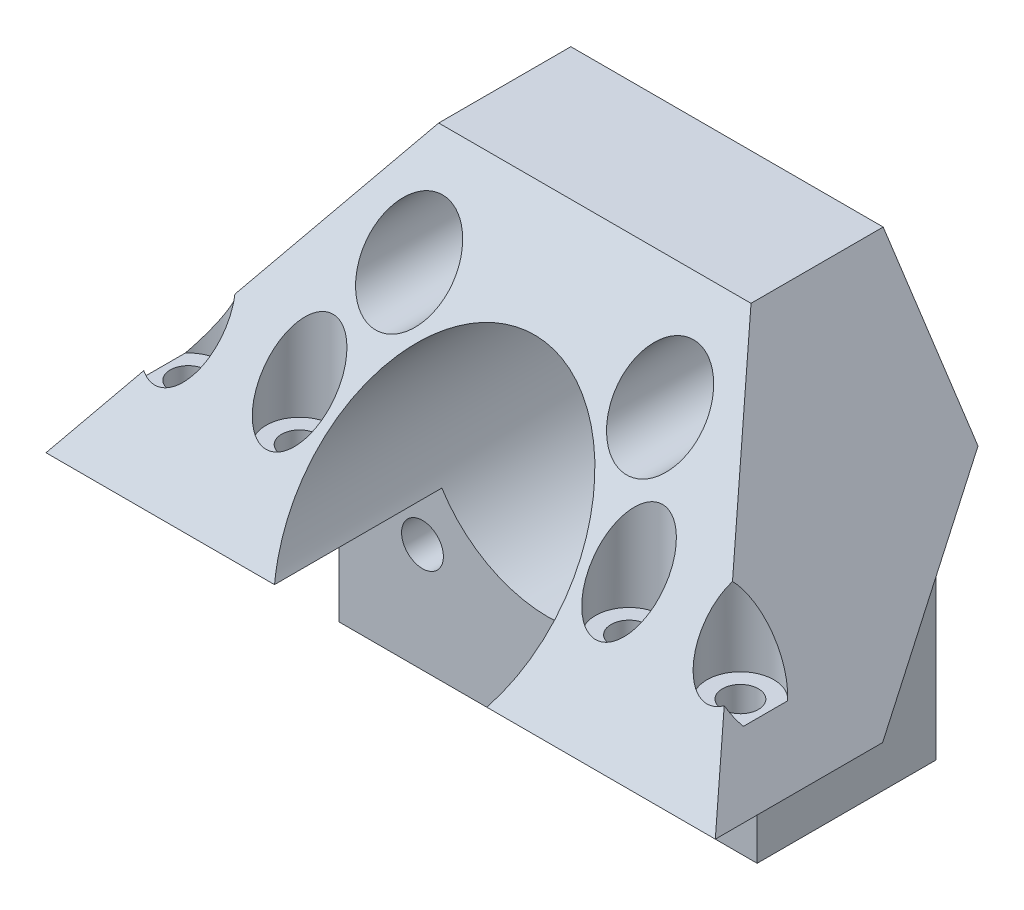
SolidWorks part; units mm, degrees
ref_plane "Front Plane" through (0, 0, 0) normal (0, 0, 1) x (1, 0, 0)
ref_plane "Top Plane" through (0, 0, 0) normal (0, 1, 0) x (1, 0, 0)
ref_plane "Right Plane" through (0, 0, 0) normal (1, 0, 0) x (0, 0, -1)
sketch "Sketch1" plane through (0, 0, 0) normal (0, 0, 1) x (1, 0, 0)
  line L1 (-10.526, 82.334) -> (-411.1387, 82.334) construction
  line L4 (-96.1387, 84.334) -> (-46.1387, 84.334)
  line L5 (-46.1387, 84.334) -> (-46.1387, 131.334)
  line L6 (-49.1387, 134.334) -> (-93.1387, 134.334)
  line L7 (-96.1387, 131.334) -> (-96.1387, 84.334)
  line L8 (-96.1387, 82.334) -> (-46.1387, 82.334)
  line L9 (-46.1387, 82.334) -> (-46.1387, 131.334)
  line L10 (-49.1387, 134.334) -> (-93.1387, 134.334)
  line L11 (-96.1387, 131.334) -> (-96.1387, 82.334)
  arc A0 (-71.1387, 95.334) -> (-71.1387, 125.334) centre (-71.1387, 110.334) ccw construction
  arc A1 (-71.1387, 125.334) -> (-71.1387, 95.334) centre (-71.1387, 110.334) ccw construction
  arc A2 (-46.1387, 131.334) -> (-49.1387, 134.334) centre (-49.1387, 131.334) ccw
  arc A3 (-93.1387, 134.334) -> (-96.1387, 131.334) centre (-93.1387, 131.334) ccw
  arc A4 (-46.1387, 131.334) -> (-49.1387, 134.334) centre (-49.1387, 131.334) ccw
  arc A5 (-93.1387, 134.334) -> (-96.1387, 131.334) centre (-93.1387, 131.334) ccw
  arc A6 (-56.1387, 127.834) -> (-56.1387, 122.834) centre (-56.1387, 125.334) ccw construction
  arc A7 (-56.1387, 122.834) -> (-56.1387, 127.834) centre (-56.1387, 125.334) ccw construction
  arc A8 (-86.1387, 122.834) -> (-86.1387, 127.834) centre (-86.1387, 125.334) ccw construction
  arc A9 (-86.1387, 127.834) -> (-86.1387, 122.834) centre (-86.1387, 125.334) ccw construction
  arc A10 (-56.1387, 97.834) -> (-56.1387, 92.834) centre (-56.1387, 95.334) ccw construction
  arc A11 (-56.1387, 92.834) -> (-56.1387, 97.834) centre (-56.1387, 95.334) ccw construction
  arc A12 (-86.1387, 97.834) -> (-86.1387, 92.834) centre (-86.1387, 95.334) ccw construction
  arc A13 (-86.1387, 92.834) -> (-86.1387, 97.834) centre (-86.1387, 95.334) ccw construction
  arc A14 (-86.1387, 92.834) -> (-86.1387, 97.834) centre (-86.1387, 95.334) ccw
  arc A15 (-86.1387, 97.834) -> (-86.1387, 92.834) centre (-86.1387, 95.334) ccw
  arc A16 (-56.1387, 92.834) -> (-56.1387, 97.834) centre (-56.1387, 95.334) ccw
  arc A17 (-56.1387, 97.834) -> (-56.1387, 92.834) centre (-56.1387, 95.334) ccw
  arc A18 (-86.1387, 127.834) -> (-86.1387, 122.834) centre (-86.1387, 125.334) ccw
  arc A19 (-86.1387, 122.834) -> (-86.1387, 127.834) centre (-86.1387, 125.334) ccw
  arc A20 (-56.1387, 122.834) -> (-56.1387, 127.834) centre (-56.1387, 125.334) ccw
  arc A21 (-56.1387, 127.834) -> (-56.1387, 122.834) centre (-56.1387, 125.334) ccw
  arc A22 (-71.1387, 125.334) -> (-71.1387, 95.334) centre (-71.1387, 110.334) ccw
  arc A23 (-71.1387, 95.334) -> (-71.1387, 125.334) centre (-71.1387, 110.334) ccw
  dimension "D1" = 0
extrude "Extrude1" add sketch "Sketch1" along normal up to vertex (21.3971 mm away)
sketch "Sketch3" plane through (0, 102.334, 0) normal (0, 1, 0) x (1, 0, 0)
  line L0 (-10.526, -21.3971) -> (-391.1387, -21.3971) construction
  line L1 (-31.1387, -21.3971) -> (-111.1387, -21.3971)
  line L2 (-31.1387, -21.3971) -> (-31.1387, -41.3971)
  line L3 (-31.1387, -41.3971) -> (-111.1387, -41.3971)
  line L4 (-111.1387, -21.3971) -> (-111.1387, -41.3971)
  line L5 (-10.526, -41.3971) -> (-411.1387, -41.3971) construction
  line L6 (-96.1387, -21.3971) -> (-96.1387, 0) construction
  line L7 (-46.1387, -21.3971) -> (-46.1387, 0) construction
  dimension "D1" = 15
  dimension "D2" = 15
ref_plane "Plane1" through (0, 117.334, 0) normal (0, 1, 0) x (1, 0, 0)
sketch "Sketch4" plane through (0, 117.334, 0) normal (0, 1, 0) x (1, 0, 0)
  line L0 (-46.1387, -21.3971) -> (-46.1387, 0) construction
  line L1 (-41.1387, 0) -> (-101.1387, 0)
  line L2 (-41.1387, 0) -> (-41.1387, -29.3971)
  line L3 (-41.1387, -29.3971) -> (-101.1387, -29.3971)
  line L4 (-101.1387, 0) -> (-101.1387, -29.3971)
  line L5 (-96.1387, -21.3971) -> (-96.1387, 0) construction
  line L6 (-96.1387, -21.3971) -> (-46.1387, -21.3971) construction
  line L7 (-96.1387, 0) -> (-46.1387, 0) construction
  dimension "D1" = 5
  dimension "D2" = 5
  dimension "D3" = 8
loft "Loft1" add profiles "Sketch4", "Sketch3"
sketch "Sketch5" plane through (25.6735, 17.1157, 0) normal (0.8321, 0.5547, 0) x (0, 0, -1)
  line L0 (-29.3971, 120.4474) -> (-15.1156, 141.9028)
  line L1 (-29.3971, 120.4474) -> (-41.3971, 102.4197) construction
  line L2 (0, 120.4474) -> (0, 141.9028)
  line L3 (0, 139.0299) -> (0, 163.4367) construction
  line L4 (0, 141.9028) -> (-15.1156, 141.9028)
  line L5 (-29.3971, 120.4474) -> (0, 120.4474)
extrude "Extrude2" add sketch "Sketch5" against normal blind 10
ref_plane "Plane2" through (-71.1387, 0, 0) normal (1, 0, 0) x (0, 0, -1)
mirror "Mirror1" about plane through (-71.1387, 0, 0) normal (1, 0, 0) of "Extrude2"
sketch "Sketch6" plane through (0, 60.1289, 75.1612) normal (0, 0.6247, 0.7809) x (1, 0, 0)
  line L0 (-101.1387, 73.2582) -> (-85.2658, 103.749)
  line L1 (-85.2658, 103.749) -> (-57.0116, 103.749)
  line L2 (-57.0116, 103.749) -> (-41.1387, 73.2582)
  line L3 (-41.1387, 73.2582) -> (-101.1387, 73.2582)
  line L4 (-94.472, 86.0645) -> (-101.1387, 73.2582) construction
  line L5 (-47.8053, 86.0645) -> (-41.1387, 73.2582) construction
extrude "Extrude3" add sketch "Sketch6" against normal blind 9
sketch "Sketch7" plane through (0, 60.1289, 75.1612) normal (0, 0.6247, 0.7809) x (1, 0, 0)
  line L1 (-98.3152, 102.6478) -> (-38.301, 102.6478)
  line L2 (-98.3152, 102.6478) -> (-98.3152, 75.8689)
  line L3 (-98.3152, 75.8689) -> (-38.301, 75.8689)
  line L4 (-38.301, 102.6478) -> (-38.301, 75.8689)
extrude "Extrude4" cut sketch "Sketch7" along normal blind 11
sketch "Sketch8" plane through (-124.1732, 82.7822, 0) normal (-0.8321, 0.5547, 0) x (0, 0, 1)
  line L1 (-21.976, 67.9862) -> (49.491, 67.9862)
  line L2 (-21.976, 67.9862) -> (-21.976, 42.9691)
  line L3 (-21.976, 42.9691) -> (49.491, 42.9691)
  line L4 (49.491, 67.9862) -> (49.491, 42.9691)
extrude "Extrude5" cut sketch "Sketch8" along normal blind 23
mirror "Mirror2" about plane through (-71.1387, 0, 0) normal (1, 0, 0) of "Extrude5"
sketch "Sketch9" plane through (0, 134.334, 0) normal (0, 1, 0) x (1, 0, 0)
  line L1 (-40.0157, 4.7519) -> (-99.9932, 4.7519)
  line L2 (-40.0157, 4.7519) -> (-40.0157, -26.1221)
  line L3 (-40.0157, -26.1221) -> (-99.9932, -26.1221)
  line L4 (-99.9932, 4.7519) -> (-99.9932, -26.1221)
extrude "Extrude6" cut sketch "Sketch9" along normal blind 7
sketch "Sketch10" plane through (0, 0, 0) normal (0, 0, -1) x (-1, 0, 0)
  arc A0 (57.8722, 117.334) -> (84.4052, 117.334) centre (71.1387, 110.334) ccw construction
  arc A1 (57.8722, 117.334) -> (58.4501, 102.334) centre (71.1387, 110.334) ccw construction
  arc A2 (84.4052, 117.334) -> (57.8722, 117.334) centre (71.1387, 110.334) ccw construction
  arc A3 (57.8722, 117.334) -> (84.4052, 117.334) centre (71.1387, 110.334) ccw
  arc A4 (57.8722, 117.334) -> (58.4501, 102.334) centre (71.1387, 110.334) ccw
  arc A5 (84.4052, 117.334) -> (57.8722, 117.334) centre (71.1387, 110.334) ccw
  circle A6 centre (56.1387, 125.334) radius 2.5
  circle A7 centre (86.1387, 125.334) radius 2.5
  arc M7 (57.8722, 117.334) -> (84.4052, 117.334) centre (71.1387, 110.334) cw
  arc M8 (84.4052, 117.334) -> (57.8722, 117.334) centre (71.1387, 110.334) cw
extrude "Extrude7" cut sketch "Sketch10" against normal blind 65 contours A3 M7 M8 | A6 | A7
ref_plane "Plane3" through (0, 0, 8) normal (0, 0, -1) x (-1, 0, 0)
sketch "Sketch12" plane through (0, 0, 8) normal (0, 0, -1) x (-1, 0, 0)
  circle A0 centre (86.1387, 125.334) radius 5
  circle A1 centre (56.1387, 125.334) radius 5
  dimension "D1" = 10
  dimension "D2" = 10
extrude "Extrude8" cut sketch "Sketch12" against normal blind 65
sketch "Sketch13" plane through (0, 102.334, 0) normal (0, -1, 0) x (1, 0, 0)
  line L0 (-111.1387, 31.3971) -> (-31.1387, 31.3971) construction
  line L1 (-111.1387, 21.3971) -> (-111.1387, 41.3971) construction
  line L2 (-31.1387, 41.3971) -> (-31.1387, 21.3971) construction
  line L3 (-83.8273, 21.3971) -> (-83.8273, 41.3971) construction
  line L4 (-58.4501, 41.3971) -> (-58.4501, 21.3971) construction
  circle A0 centre (-104.1387, 31.3971) radius 2.15
  circle A1 centre (-90.8273, 31.3971) radius 2.15
  circle A2 centre (-51.4501, 31.3971) radius 2.15
  circle A3 centre (-38.1387, 31.3971) radius 2.15
  dimension "D1" = 4.3
  dimension "D2" = 7
  dimension "D3" = 7
  dimension "D4" = 7
  dimension "D5" = 7
extrude "Extrude9" cut sketch "Sketch13" against normal blind 65
ref_plane "Plane4" through (0, 108.334, 0) normal (0, -1, 0) x (-1, 0, 0)
sketch "Sketch14" plane through (0, 108.334, 0) normal (0, -1, 0) x (-1, 0, 0)
  circle A0 centre (104.1387, -31.3971) radius 4
  circle A1 centre (90.8273, -31.3971) radius 4
  circle A2 centre (51.4501, -31.3971) radius 4
  circle A3 centre (38.1387, -31.3971) radius 4
  dimension "D1" = 8
extrude "Extrude10" cut sketch "Sketch14" against normal blind 65
